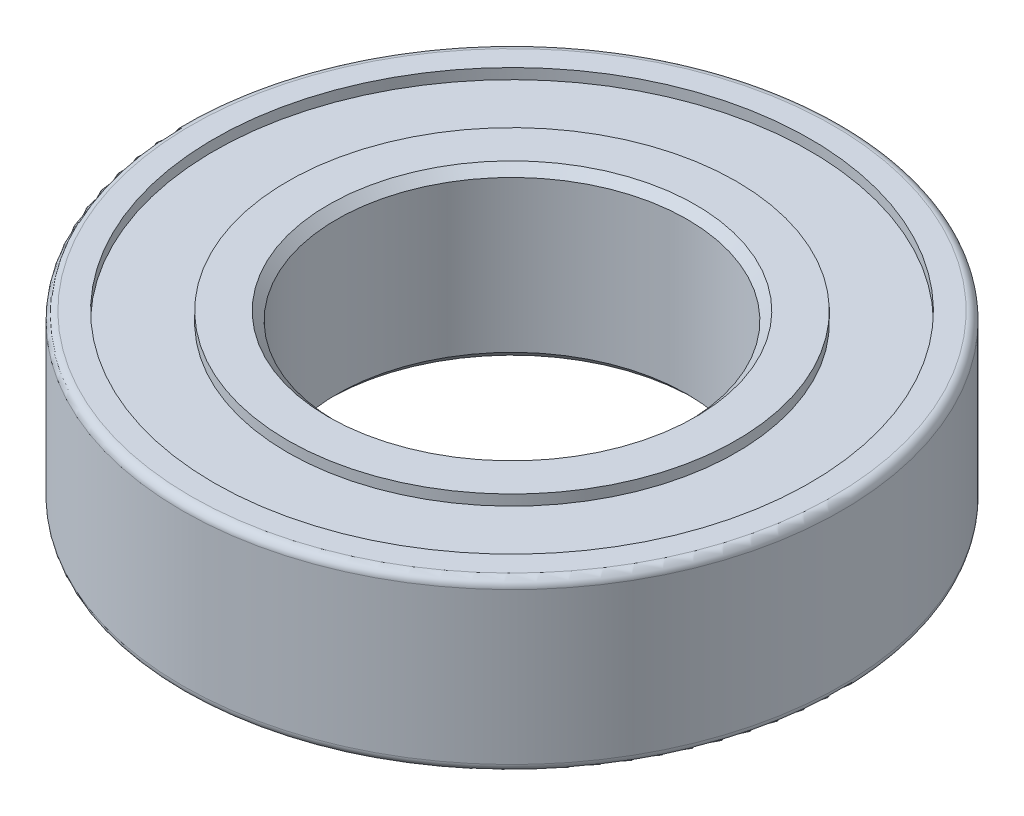
SolidWorks part; units mm, degrees
ref_plane "Front Plane" through (0, 0, 0) normal (0, 0, 1) x (1, 0, 0)
ref_plane "Top Plane" through (0, 0, 0) normal (0, 1, 0) x (1, 0, 0)
ref_plane "Right Plane" through (0, 0, 0) normal (1, 0, 0) x (0, 0, -1)
sketch "Sketch1" plane through (0, 0, 0) normal (1, 0, 0) x (0, 0, -1)
  line L0 (0, 26.6807) -> (0, -26.6807) construction
  line L1 (-13.1, 6) -> (-12.5, 5.4)
  line L2 (-22.9, 6) -> (-21.25, 6)
  line L3 (-23.5, 5.4) -> (-23.5, -5.4)
  line L4 (-22.9, -6) -> (-21.25, -6)
  line L5 (-12.5, 5.4) -> (-12.5, -5.4)
  line L6 (-23.5, 6) -> (-12.5, -6) construction
  line L7 (-23.5, -6) -> (-12.5, 6) construction
  line L8 (-13.1, -6) -> (-12.5, -5.4)
  line L9 (0, 0) -> (-31.6606, 0) construction
  line L10 (-21.25, 6) -> (-21.25, 5.25)
  line L11 (-21.25, 5.25) -> (-16, 5.25)
  line L12 (-16, 5.25) -> (-16, 6)
  line L13 (-16, 6) -> (-13.1, 6)
  line L14 (-16, -5.25) -> (-16, -6)
  line L15 (-21.25, -5.25) -> (-16, -5.25)
  line L16 (-21.25, -6) -> (-21.25, -5.25)
  line L17 (-16, -6) -> (-13.1, -6)
  arc A0 (-23.5, -5.4) -> (-22.9, -6) centre (-22.9, -5.4) ccw
  arc A1 (-22.9, 6) -> (-23.5, 5.4) centre (-22.9, 5.4) ccw
  point P3 (-18, 0)
  dimension "D4" = 0.6
  dimension "D1" = 12
  dimension "D2" = 25
  dimension "D3" = 47
  dimension "D5" = 42.5
  dimension "D6" = 32
  dimension "D7" = 0.75
revolve "Revolve1" add sketch "Sketch1" angle 360 about L0
